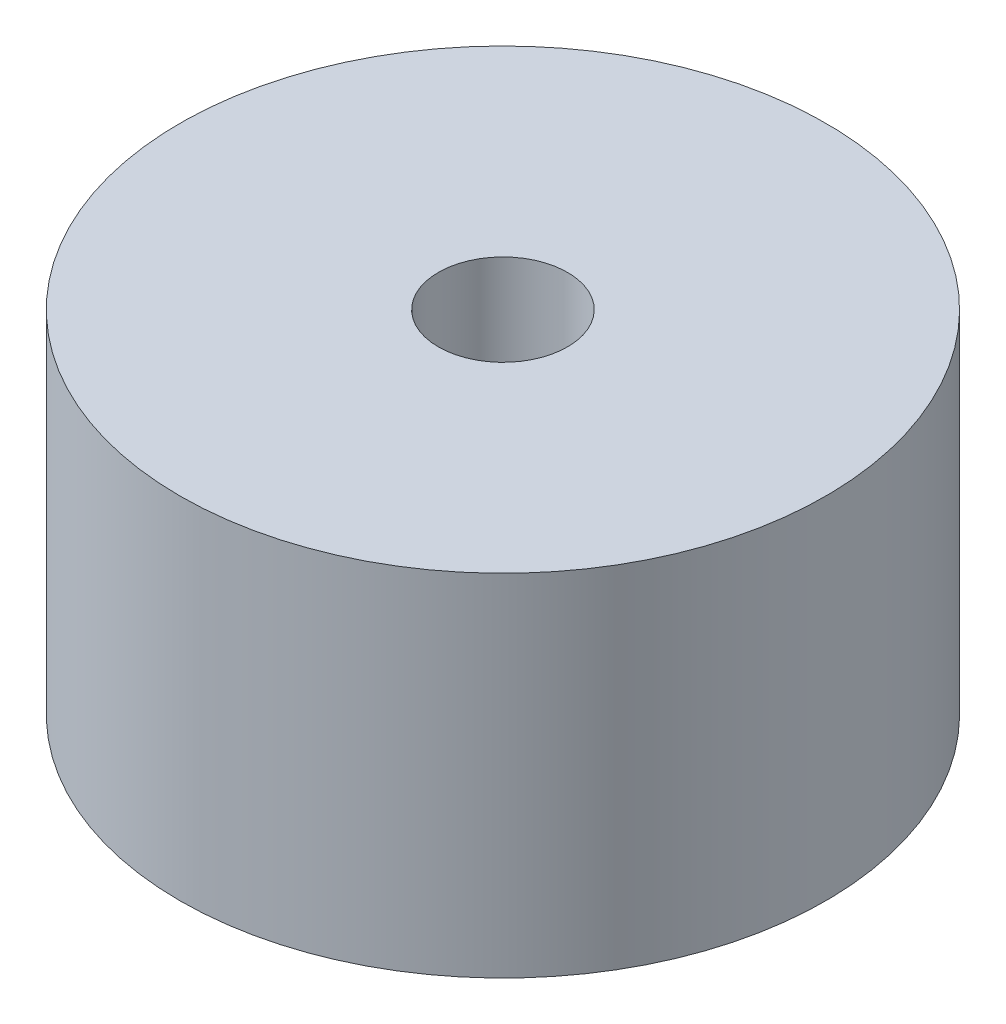
SolidWorks part; units mm, degrees
ref_plane "Plano frontal" through (0, 0, 0) normal (0, 0, 1) x (1, 0, 0)
ref_plane "Plano superior" through (0, 0, 0) normal (0, 1, 0) x (1, 0, 0)
ref_plane "Plano direito" through (0, 0, 0) normal (1, 0, 0) x (0, 0, -1)
sketch "Sketch1" plane through (0, 0, 0) normal (0, 0, 1) x (1, 0, 0)
  line L0 (7, 30.3265) -> (7, 10.3265)
  line L1 (7, 10.3265) -> (25, -7.6735)
  line L2 (25, -7.6735) -> (35, -7.6735)
  line L3 (35, -7.6735) -> (35, 30.3265)
  line L4 (35, 30.3265) -> (7, 30.3265)
  line L5 (0, 50.5681) -> (0, -63.6641) construction
  dimension "D1" = 20
  dimension "D2" = 135
  dimension "D3" = 7
  dimension "D4" = 25
  dimension "D5" = 35
revolve "Revolve1" add sketch "Sketch1" angle 360 about L5
